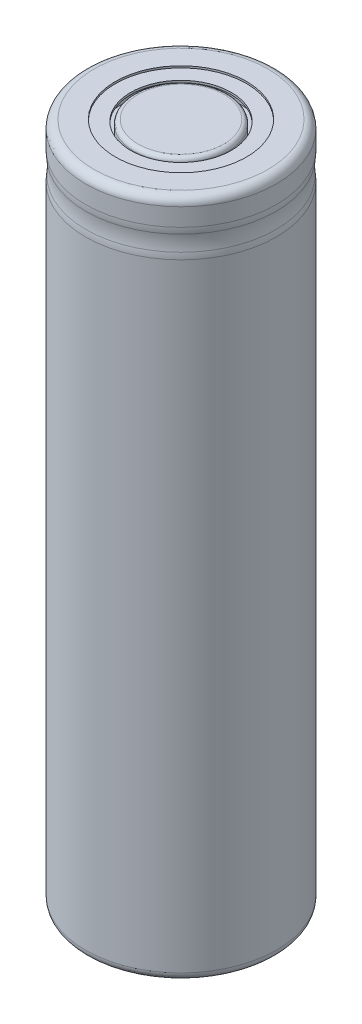
SolidWorks part; units mm, degrees
ref_plane "Plan de face" through (0, 0, 0) normal (0, 0, 1) x (1, 0, 0)
ref_plane "Plan de dessus" through (0, 0, 0) normal (0, 1, 0) x (1, 0, 0)
ref_plane "Plan de droite" through (0, 0, 0) normal (1, 0, 0) x (0, 0, -1)
sketch "Esquisse1" plane through (0, 0, 0) normal (0, 0, 1) x (1, 0, 0)
  line L0 (0, 0) -> (0, 64.88) construction
  line L1 (0, 64.88) -> (4.5, 64.88)
  line L2 (4.5, 64.88) -> (4.5, 63.1476)
  line L3 (4.5, 63.1476) -> (5.7885, 63.1476)
  line L4 (4.8, 64.7) -> (4.8, 64.5)
  line L5 (4.8, 64.7) -> (6.25, 64.7)
  line L6 (6.25, 64.7) -> (6.25, 64.88)
  line L7 (6.25, 64.88) -> (9.1, 64.88)
  line L8 (9.1, 64.88) -> (9.1, 0)
  line L9 (9.1, 0) -> (7, 0)
  line L10 (7, 0) -> (7, 0.18)
  line L11 (7, 0.18) -> (0, 0.18)
  line L12 (4.8, 64.5) -> (5.7885, 64.5)
  line L13 (5.7885, 64.5) -> (5.7885, 63.1476)
  line L14 (0, 64.88) -> (0, 0.18)
  dimension "D1" = 64.7
  dimension "D2" = 0.18
  dimension "D3" = 9
  dimension "D4" = 0.18
  dimension "D5" = 0.3
  dimension "D6" = 0.2
  dimension "D7" = 12.5
  dimension "D8" = 18.2
  dimension "D9" = 14
revolve "Révolution1" add sketch "Esquisse1" angle 360 about L0
fillet "Congé1" radius 0.4 1 edges at (0, 64.88, -4.5)
fillet "Congé2" radius 0.8 2 edges at (0, 0, -9.1) (0, 64.88, -9.1)
sketch "Esquisse2" plane through (0, 0, 0) normal (1, 0, 0) x (0, 0, -1)
  line L0 (-15.6959, 61.04) -> (21.4339, 61.04) construction
  line L1 (0, 52.4531) -> (0, 71.9207) construction
  line L2 (9.1, 62.04) -> (9.1, 60.04) construction
  line L3 (9.1, 0.8) -> (9.1, 64.08) construction
  line L5 (6.25, 64.88) -> (-6.25, 64.88) construction
  line L6 (9, 63.1446) -> (9, 58.7599) construction
  circle A0 centre (14.05, 61.04) radius 5.05
  dimension "D4" = 0.1
  dimension "D1" = 3.84
  dimension "D2" = 1
  dimension "D3" = 1
revolve "Enlèvement de matière-Révolution1" cut sketch "Esquisse2" angle 360 about L1
fillet "Congé3" radius 4 2 edges at (0, 60.04, 9.1) (0, 62.04, -9.1)
